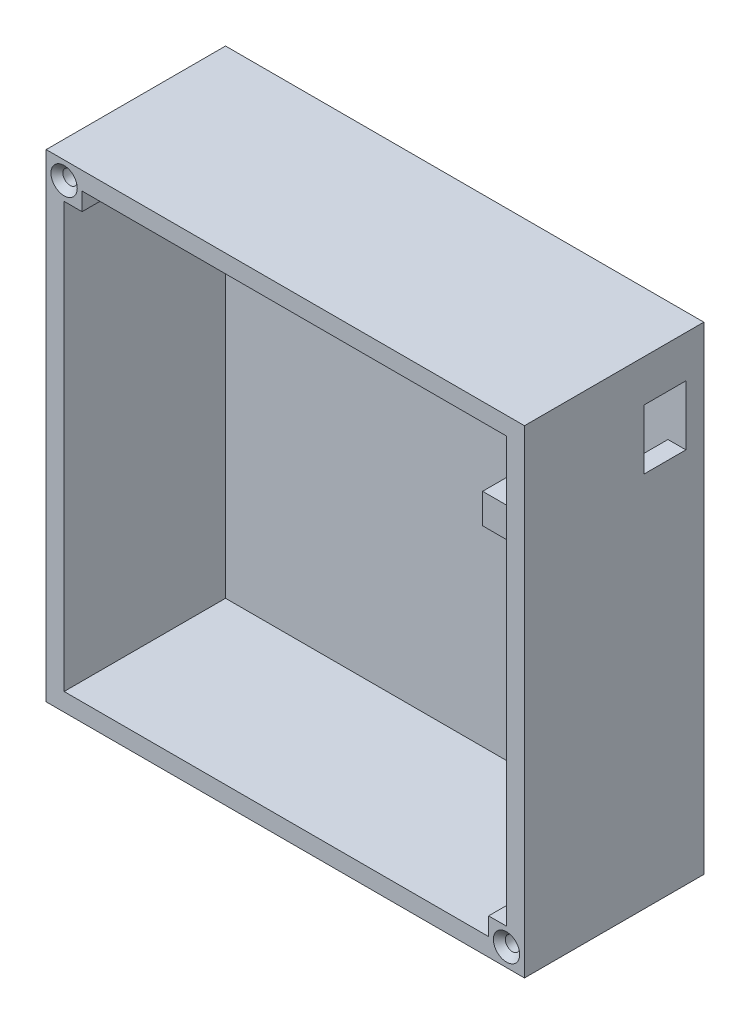
SolidWorks part; units mm, degrees
ref_plane "Front Plane" through (0, 0, 0) normal (0, 0, 1) x (1, 0, 0)
ref_plane "Top Plane" through (0, 0, 0) normal (0, 1, 0) x (1, 0, 0)
ref_plane "Right Plane" through (0, 0, 0) normal (1, 0, 0) x (0, 0, -1)
sketch "Sketch1" plane through (0, 0, 0) normal (0, 0, 1) x (1, 0, 0)
  line L1 (0, 0) -> (80, 0)
  line L2 (0, 0) -> (0, 80)
  line L3 (0, 80) -> (80, 80)
  line L4 (80, 0) -> (80, 80)
extrude "Boss-Extrude1" add sketch "Sketch1" along normal blind 30 contours L3 L4 L1 L2
sketch "Sketch2" plane through (0, 0, 30) normal (0, 0, 1) x (1, 0, 0)
  line L7 (3, 77) -> (77, 77)
  line L8 (3, 77) -> (3, 3)
  line L9 (3, 3) -> (77, 3)
  line L10 (77, 77) -> (77, 3)
extrude "Cut-Extrude1" cut sketch "Sketch2" against normal blind 27
sketch "Sketch3" plane through (80, 0, 0) normal (1, 0, 0) x (0, 0, -1)
  line L4 (-3, 68) -> (-3, 63)
  line L5 (-3, 68) -> (-3, 73)
  line L6 (-3, 73) -> (-10, 73)
  line L7 (-10, 68) -> (-10, 73)
  line L8 (-3, 63) -> (-10, 63)
  line L9 (-10, 68) -> (-10, 63)
  point P2 (0, 0)
  point P5 (0, 0)
  point P6 (0, 0)
  point P7 (0, 0)
  point P8 (0, 0)
  point P9 (0, 0)
  point P10 (0, 0)
  point P11 (0, 0)
  point P12 (0, 0)
extrude "Cut-Extrude2" cut sketch "Sketch3" against normal blind 3
sketch "Sketch5" plane through (0, 0, 3) normal (0, 0, 1) x (1, 0, 0)
  line L1 (3, 77) -> (6, 77)
  line L2 (3, 77) -> (3, 74)
  line L3 (3, 74) -> (6, 74)
  line L4 (6, 77) -> (6, 74)
extrude "Boss-Extrude3" add sketch "Sketch5" along normal blind 27
sketch "Sketch6" plane through (0, 0, 3) normal (0, 0, 1) x (1, 0, 0)
  line L1 (77, 3) -> (74, 3)
  line L2 (77, 3) -> (77, 6)
  line L3 (77, 6) -> (74, 6)
  line L4 (74, 3) -> (74, 6)
extrude "Boss-Extrude4" add sketch "Sketch6" along normal blind 27
hole_wizard "CSK for M2 Countersunk Flat Head Screw1" positions "Sketch7" profile "Sketch8" countersink size "M2" standard "DIN" end condition through all
sketch "Sketch7" plane through (0, 0, 30) normal (0, 0, 1) x (1, 0, 0)
  point P0 (3, 77)
  point P2 (77, 3)
sketch "Sketch8" plane through (3, 77, 30) normal (1, 0, 0) x (0, -1, 0)
  line L0 (0, 0) -> (0, 30)
  line L1 (0, 30) -> (1.2, 30)
  line L2 (1.2, 30) -> (1.2, 1)
  line L3 (1.2, 1) -> (2.2, 0)
  line L5 (2.2, 0) -> (0, 0)
  line L6 (-1.2, 1) -> (-2.2, 0) construction
  line L11 (0, -6.35) -> (0, 107.95) construction
  dimension "Thru Hole Dia." = 2.4
  dimension "Thru Hole Depth" = 30
  dimension "Near C'Sink Dia." = 4.4
  dimension "Near C'Sink Angle" = 90
sketch "Sketch9" plane through (0, 0, 3) normal (0, 0, 1) x (1, 0, 0)
  line L5 (50, 68) -> (50, 69)
  line L6 (50, 69) -> (47.5388, 69)
  line L7 (47.5388, 68) -> (47.5388, 69)
  line L9 (47.5388, 68) -> (47.5388, 67)
  line L10 (47.5388, 67) -> (50, 67)
  line L11 (50, 68) -> (50, 67)
extrude "Boss-Extrude5" add sketch "Sketch9" along normal blind 3 contours L6 L7 L9 L10 L11 L5
sketch "Sketch10" plane through (0, 0, 3) normal (0, 0, 1) x (1, 0, 0)
  line L3 (70, 59) -> (65, 59)
  line L4 (70, 59) -> (70, 54)
  line L5 (70, 54) -> (65, 54)
  line L6 (65, 59) -> (65, 54)
extrude "Boss-Extrude6" add sketch "Sketch10" along normal blind 19 contours L3 L6 L5 L4
